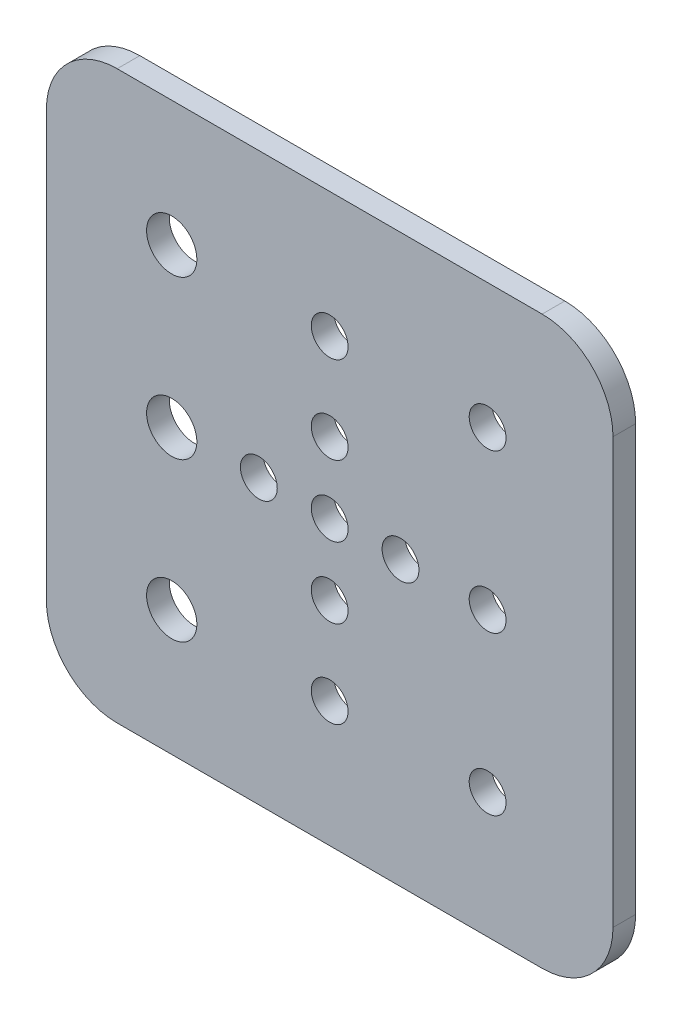
SolidWorks part; units mm, degrees
ref_plane "Front Plane" through (0, 0, 0) normal (0, 0, 1) x (1, 0, 0)
ref_plane "Top Plane" through (0, 0, 0) normal (0, 1, 0) x (1, 0, 0)
ref_plane "Right Plane" through (0, 0, 0) normal (1, 0, 0) x (0, 0, -1)
sketch "Sketch1" plane through (0, 0, 0) normal (0, 0, 1) x (1, 0, 0)
  line L0 (0, 40) -> (0, -40) construction
  line L1 (-40, 40) -> (40, 40)
  line L2 (-40, 40) -> (-40, -40)
  line L3 (-40, -40) -> (40, -40)
  line L4 (40, 40) -> (40, -40)
  line L5 (-40, 40) -> (40, -40) construction
  line L6 (-40, -40) -> (40, 40) construction
  line L7 (-40, 0) -> (40, 0) construction
  circle A0 centre (0, 0) radius 2.6
  circle A1 centre (0, 10) radius 2.6
  circle A2 centre (0, 22.3) radius 2.6
  circle A3 centre (0, -10) radius 2.6
  circle A4 centre (0, -22.3) radius 2.6
  circle A5 centre (10, 0) radius 2.6
  circle A6 centre (-10, 0) radius 2.6
  circle A7 centre (-22.3, 0) radius 3.55
  circle A8 centre (22.3, 0) radius 2.6
  circle A9 centre (22.3, 22.3) radius 2.6
  circle A10 centre (22.3, -22.3) radius 2.6
  circle A11 centre (-22.3, -22.3) radius 3.55
  circle A12 centre (-22.3, 22.3) radius 3.55
  point P0 (0, 0)
  dimension "D3" = 7.1
  dimension "D4" = 5.2
  dimension "D1" = 80
  dimension "D2" = 80
  dimension "D5" = 10
  dimension "D6" = 10
  dimension "D7" = 12.3
  dimension "D8" = 12.3
  dimension "D9" = 10
  dimension "D10" = 12.3
  dimension "D11" = 10
extrude "Boss-Extrude1" add sketch "Sketch1" along normal blind 3.2
fillet "Fillet1" radius 10 4 edges at (-40, -40, 1.6) (40, -40, 1.6) (40, 40, 1.6) (-40, 40, 1.6)
